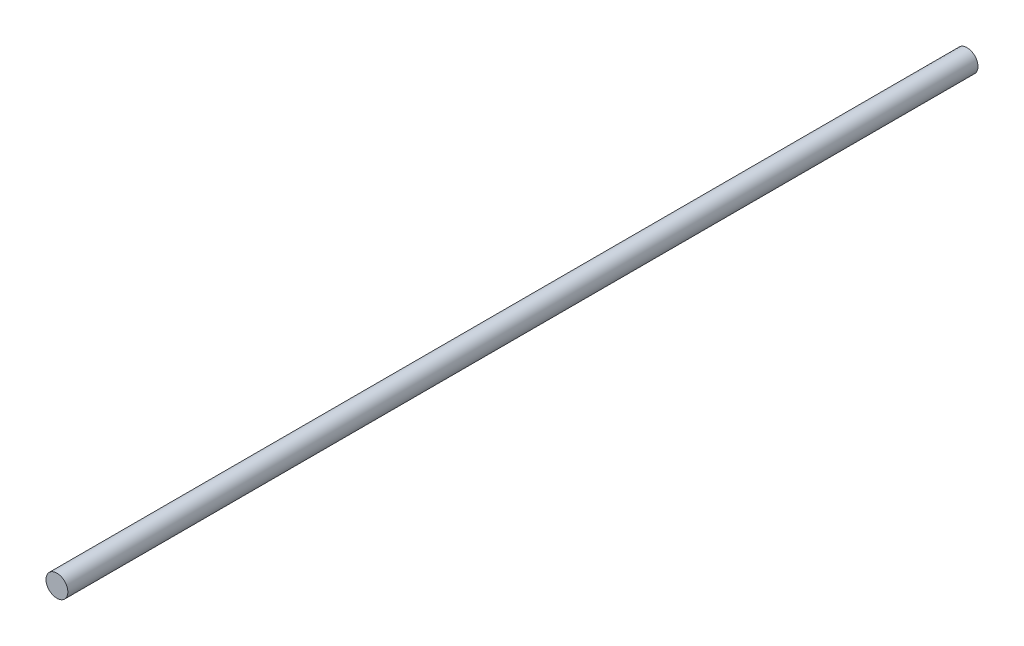
SolidWorks part; units mm, degrees
ref_plane "Plan de face" through (0, 0, 0) normal (0, 0, 1) x (1, 0, 0)
ref_plane "Plan de dessus" through (0, 0, 0) normal (0, 1, 0) x (1, 0, 0)
ref_plane "Plan de droite" through (0, 0, 0) normal (1, 0, 0) x (0, 0, -1)
sketch "Esquisse1" plane through (0, 0, 0) normal (0, 0, 1) x (1, 0, 0)
  circle A0 centre (0, 0) radius 3
  dimension "D1" = 6
extrude "Boss.-Extru.1" add sketch "Esquisse1" along normal blind 250
